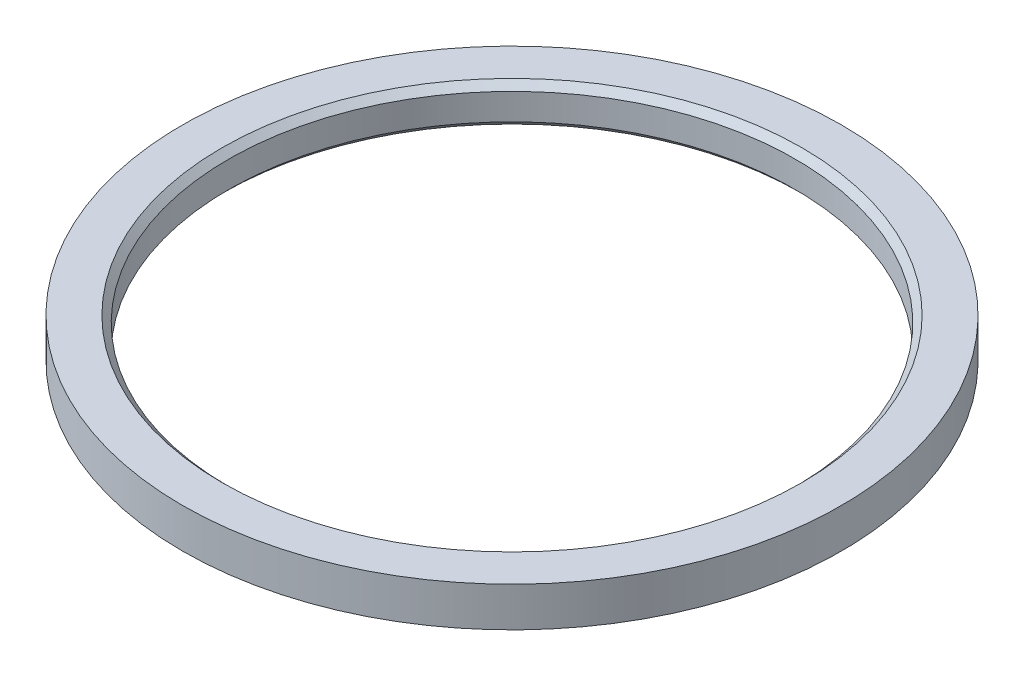
SolidWorks part; units mm, degrees
ref_plane "前视基准面" through (0, 0, 0) normal (0, 0, 1) x (1, 0, 0)
ref_plane "上视基准面" through (0, 0, 0) normal (0, 1, 0) x (1, 0, 0)
ref_plane "右视基准面" through (0, 0, 0) normal (1, 0, 0) x (0, 0, -1)
sketch "草图1" plane through (0, 0, 0) normal (0, 1, 0) x (1, 0, 0)
  circle A0 centre (0, 0) radius 8.6
  circle A1 centre (0, 0) radius 10
  dimension "D1" = 17.2
  dimension "D2" = 20
extrude "凸台-拉伸1" add sketch "草图1" along normal blind 1.2
chamfer "倒角1" distance 0.2 angle 45 2 edges at (0, 0, 8.6) (0, 1.2, 8.6)
